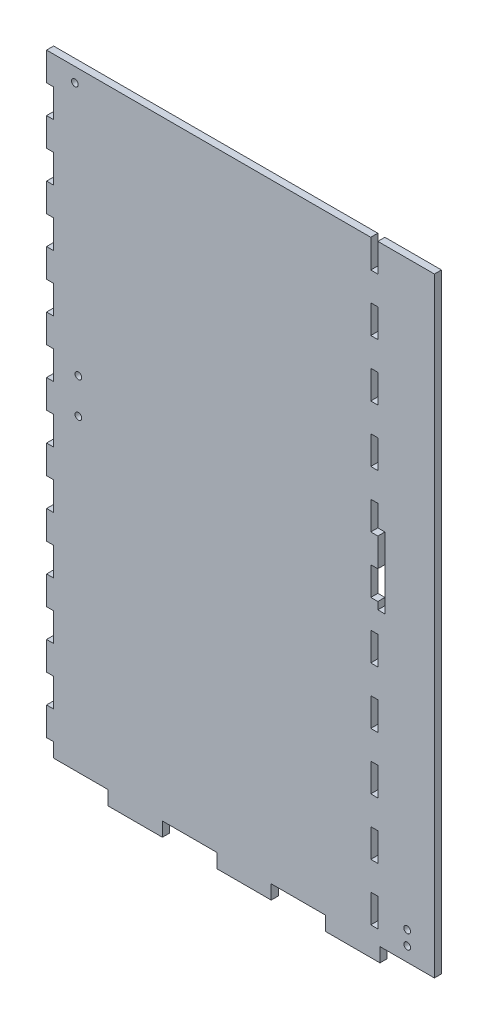
SolidWorks part; units mm, degrees
ref_plane "Front Plane" through (0, 0, 0) normal (0, 0, 1) x (1, 0, 0)
ref_plane "Top Plane" through (0, 0, 0) normal (0, 1, 0) x (1, 0, 0)
ref_plane "Right Plane" through (0, 0, 0) normal (1, 0, 0) x (0, 0, -1)
sketch "Sketch1" plane through (0, 0, 0) normal (0, 0, 1) x (1, 0, 0)
  line L0 (24.4294, -140.081) -> (24.4294, -133.731)
  line L1 (0, -140.081) -> (171.0055, -140.081)
  line L2 (0, -140.081) -> (0, 140.081)
  line L3 (0, 140.081) -> (171.0055, 140.081)
  line L4 (171.0055, -140.081) -> (171.0055, 140.081)
  line L5 (0, -140.081) -> (24.4294, -140.081)
  line L6 (0, -140.081) -> (0, -133.731)
  line L7 (0, -133.731) -> (24.4294, -133.731)
  line L8 (24.4294, -140.081) -> (24.4294, -133.731)
  line L9 (24.4294, -140.081) -> (48.8587, -140.081)
  line L10 (48.8587, -140.081) -> (48.8587, -133.731)
  line L11 (24.4294, -133.731) -> (48.8587, -133.731)
  line L12 (48.8587, -140.081) -> (48.8587, -133.731)
  line L13 (48.8587, -140.081) -> (73.2881, -140.081)
  line L14 (73.2881, -140.081) -> (73.2881, -133.731)
  line L15 (48.8587, -133.731) -> (73.2881, -133.731)
  line L16 (73.2881, -140.081) -> (73.2881, -133.731)
  line L17 (73.2881, -140.081) -> (97.7174, -140.081)
  line L18 (97.7174, -140.081) -> (97.7174, -133.731)
  line L19 (73.2881, -133.731) -> (97.7174, -133.731)
  line L20 (97.7174, -140.081) -> (97.7174, -133.731)
  line L21 (97.7174, -140.081) -> (122.1468, -140.081)
  line L22 (122.1468, -140.081) -> (122.1468, -133.731)
  line L23 (97.7174, -133.731) -> (122.1468, -133.731)
  line L24 (122.1468, -140.081) -> (122.1468, -133.731)
  line L25 (122.1468, -140.081) -> (146.5761, -140.081)
  line L26 (146.5761, -140.081) -> (146.5761, -133.731)
  line L27 (122.1468, -133.731) -> (146.5761, -133.731)
  line L28 (146.5761, -140.081) -> (146.5761, -133.731)
  line L29 (146.5761, -140.081) -> (171.0055, -140.081)
  line L30 (171.0055, -140.081) -> (171.0055, -133.731)
  line L31 (146.5761, -133.731) -> (171.0055, -133.731)
  line L32 (0, 114.6117) -> (0, 101.8771)
  line L33 (0, 140.081) -> (-3.175, 140.081)
  line L34 (0, 140.081) -> (0, 127.3464)
  line L35 (0, 127.3464) -> (-3.175, 127.3464)
  line L36 (-3.175, 140.081) -> (-3.175, 127.3464)
  line L37 (0, 114.6117) -> (-3.175, 114.6117)
  line L38 (-3.175, 114.6117) -> (-3.175, 101.8771)
  line L39 (0, 101.8771) -> (-3.175, 101.8771)
  line L40 (0, 89.1425) -> (0, 76.4078)
  line L41 (0, 89.1425) -> (-3.175, 89.1425)
  line L42 (-3.175, 89.1425) -> (-3.175, 76.4078)
  line L43 (0, 76.4078) -> (-3.175, 76.4078)
  line L44 (0, 63.6732) -> (0, 50.9385)
  line L45 (0, 63.6732) -> (-3.175, 63.6732)
  line L46 (-3.175, 63.6732) -> (-3.175, 50.9385)
  line L47 (0, 50.9385) -> (-3.175, 50.9385)
  line L48 (0, 38.2039) -> (0, 25.4693)
  line L49 (0, 38.2039) -> (-3.175, 38.2039)
  line L50 (-3.175, 38.2039) -> (-3.175, 25.4693)
  line L51 (0, 25.4693) -> (-3.175, 25.4693)
  line L52 (0, 12.7346) -> (0, 0)
  line L53 (0, 12.7346) -> (-3.175, 12.7346)
  line L54 (-3.175, 12.7346) -> (-3.175, 0)
  line L55 (0, 0) -> (-3.175, 0)
  line L56 (0, -12.7346) -> (0, -25.4693)
  line L57 (0, -12.7346) -> (-3.175, -12.7346)
  line L58 (-3.175, -12.7346) -> (-3.175, -25.4693)
  line L59 (0, -25.4693) -> (-3.175, -25.4693)
  line L60 (0, -38.2039) -> (0, -50.9385)
  line L61 (0, -38.2039) -> (-3.175, -38.2039)
  line L62 (-3.175, -38.2039) -> (-3.175, -50.9385)
  line L63 (0, -50.9385) -> (-3.175, -50.9385)
  line L64 (0, -63.6732) -> (0, -76.4078)
  line L65 (0, -63.6732) -> (-3.175, -63.6732)
  line L66 (-3.175, -63.6732) -> (-3.175, -76.4078)
  line L67 (0, -76.4078) -> (-3.175, -76.4078)
  line L68 (0, -89.1425) -> (0, -101.8771)
  line L69 (0, -89.1425) -> (-3.175, -89.1425)
  line L70 (-3.175, -89.1425) -> (-3.175, -101.8771)
  line L71 (0, -101.8771) -> (-3.175, -101.8771)
  line L72 (0, -114.6117) -> (0, -127.3464)
  line L73 (0, -114.6117) -> (-3.175, -114.6117)
  line L74 (-3.175, -114.6117) -> (-3.175, -127.3464)
  line L75 (0, -127.3464) -> (-3.175, -127.3464)
  line L76 (71.2152, 140.081) -> (71.2152, -140.081) construction
  line L121 (-3.175, 6.3673) -> (145.6055, 6.3673) construction
  line L122 (142.4305, -127.3464) -> (145.6055, -127.3464)
  line L128 (145.6055, -114.6117) -> (145.6055, -127.3464)
  line L129 (142.4305, -114.6117) -> (145.6055, -114.6117)
  line L130 (142.4305, -114.6117) -> (142.4305, -127.3464)
  line L131 (142.4305, -101.8771) -> (145.6055, -101.8771)
  line L132 (145.6055, -89.1425) -> (145.6055, -101.8771)
  line L133 (142.4305, -89.1425) -> (145.6055, -89.1425)
  line L134 (142.4305, -89.1425) -> (142.4305, -101.8771)
  line L135 (142.4305, -76.4078) -> (145.6055, -76.4078)
  line L136 (145.6055, -63.6732) -> (145.6055, -76.4078)
  line L137 (142.4305, -63.6732) -> (145.6055, -63.6732)
  line L138 (142.4305, -63.6732) -> (142.4305, -76.4078)
  line L139 (142.4305, -50.9385) -> (145.6055, -50.9385)
  line L140 (145.6055, -38.2039) -> (145.6055, -50.9385)
  line L141 (142.4305, -38.2039) -> (145.6055, -38.2039)
  line L142 (142.4305, -38.2039) -> (142.4305, -50.9385)
  line L143 (142.4305, -25.4693) -> (145.6055, -25.4693)
  line L144 (145.6055, -12.7346) -> (145.6055, -25.4693)
  line L145 (142.4305, -12.7346) -> (145.6055, -12.7346)
  line L146 (142.4305, -12.7346) -> (142.4305, -25.4693)
  line L147 (142.4305, 0) -> (145.6055, 0)
  line L148 (145.6055, 12.7346) -> (145.6055, 0)
  line L149 (142.4305, 12.7346) -> (145.6055, 12.7346)
  line L150 (142.4305, 12.7346) -> (142.4305, 0)
  line L151 (142.4305, 25.4693) -> (145.6055, 25.4693)
  line L152 (145.6055, 38.2039) -> (145.6055, 25.4693)
  line L153 (142.4305, 38.2039) -> (145.6055, 38.2039)
  line L154 (142.4305, 38.2039) -> (142.4305, 25.4693)
  line L155 (142.4305, 50.9385) -> (145.6055, 50.9385)
  line L156 (145.6055, 63.6732) -> (145.6055, 50.9385)
  line L157 (142.4305, 63.6732) -> (145.6055, 63.6732)
  line L158 (142.4305, 63.6732) -> (142.4305, 50.9385)
  line L159 (142.4305, 76.4078) -> (145.6055, 76.4078)
  line L160 (145.6055, 89.1425) -> (145.6055, 76.4078)
  line L161 (142.4305, 89.1425) -> (145.6055, 89.1425)
  line L162 (142.4305, 89.1425) -> (142.4305, 76.4078)
  line L163 (142.4305, 101.8771) -> (145.6055, 101.8771)
  line L164 (145.6055, 114.6117) -> (145.6055, 101.8771)
  line L165 (142.4305, 114.6117) -> (145.6055, 114.6117)
  line L166 (145.6055, 140.081) -> (145.6055, 127.3464)
  line L167 (142.4305, 127.3464) -> (145.6055, 127.3464)
  line L168 (142.4305, 140.081) -> (142.4305, 127.3464)
  line L169 (142.4305, 140.081) -> (145.6055, 140.081)
  line L170 (142.4305, 114.6117) -> (142.4305, 101.8771)
  point P4 (0, 0)
  point P6 (71.2153, 6.3673)
  dimension "D1" = 280.162
  dimension "D2" = 171.0055
  dimension "D3" = 6.35
  dimension "D5" = 24.4294
  dimension "D6" = 3.175
  dimension "D8" = 12.7346
  dimension "D9" = 12.7346
  dimension "D12" = 148.7805
  dimension "D4" = 7
  dimension "D7" = 11
extrude "Boss-Extrude1" add sketch "Sketch1" along normal blind 3.175
sketch "Sketch2" plane through (0, 0, 3.175) normal (0, 0, 1) x (1, 0, 0)
  line L0 (11.1125, 20.574) -> (11.1125, 4.826) construction
  line L1 (24.4294, -140.081) -> (48.8587, -140.081) construction
  line L3 (-3.175, 140.081) -> (-3.175, 127.3464) construction
  line L4 (0, 12.7346) -> (-3.175, 12.7346) construction
  line L6 (146.5761, -133.731) -> (171.0055, -133.731) construction
  line L7 (-3.175, 140.081) -> (142.4305, 140.081) construction
  line L8 (145.6055, 38.2039) -> (145.6055, 25.4693) construction
  line L9 (145.6055, 28.6385) -> (148.7805, 28.6385)
  line L10 (145.6055, 28.6385) -> (145.6055, -3.2385)
  line L11 (145.6055, -3.2385) -> (148.7805, -3.2385)
  line L12 (148.7805, 28.6385) -> (148.7805, -3.2385)
  line L13 (145.6055, 12.7) -> (11.1125, 12.7) construction
  circle A0 centre (158.7908, -121.031) radius 1.5
  circle A1 centre (11.1125, 20.574) radius 1.5
  circle A2 centre (11.1125, 4.826) radius 1.5
  circle A3 centre (158.7908, -127.381) radius 1.5
  circle A4 centre (9.525, 133.731) radius 1.5
  point P6 (11.1125, 12.7)
  point P17 (158.7908, -133.731)
  point P28 (0, 0)
  point P31 (-1.5875, 12.7346)
  dimension "D1" = 3
  dimension "D2" = 152.781
  dimension "D3" = 12.7
  dimension "D4" = 15.748
  dimension "D5" = 12.7
  dimension "D6" = 6.35
  dimension "D7" = 6.35
  dimension "D8" = 3.175
  dimension "D9" = 31.877
  dimension "D10" = 12.7
extrude "Cut-Extrude1" cut sketch "Sketch2" against normal through all
equation "\"D5@Sketch1\"=\"D2@Sketch1\"/\"D4@Sketch1\""
equation "\"D8@Sketch1\"=\"D1@Sketch1\"/22"
equation "\"D9@Sketch1\"=\"D8@Sketch1\""
